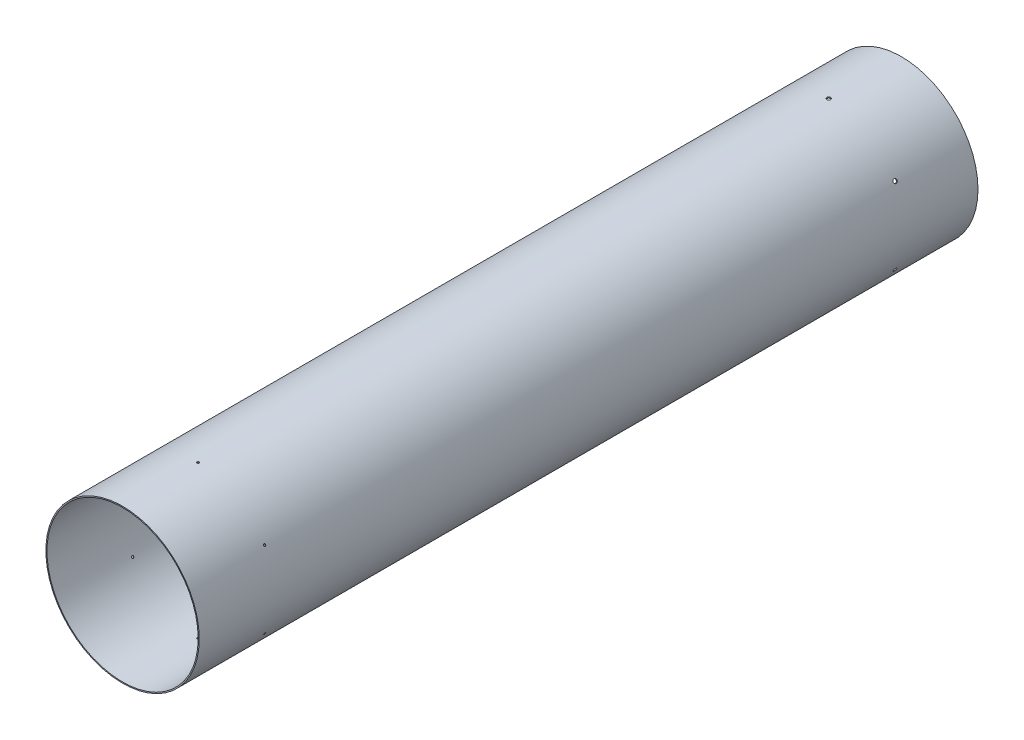
SolidWorks part; units mm, degrees
ref_plane "Front Plane" through (0, 0, 0) normal (0, 0, 1) x (1, 0, 0)
ref_plane "Top Plane" through (0, 0, 0) normal (0, 1, 0) x (1, 0, 0)
ref_plane "Right Plane" through (0, 0, 0) normal (1, 0, 0) x (0, 0, -1)
sketch "Sketch1" plane through (0, 0, 0) normal (0, 0, 1) x (1, 0, 0)
  circle A0 centre (0, 0) radius 79.375
  circle A1 centre (0, 0) radius 80.518
  dimension "D1" = 158.75
  dimension "D2" = 1.143
extrude "Boss-Extrude1" add sketch "Sketch1" along normal blind 817.5625
ref_plane "Plane1" through (0, 80.518, 0) normal (0, 1, 0) x (1, 0, 0)
sketch "Sketch2" plane through (0, 80.518, 0) normal (0, 1, 0) x (1, 0, 0)
  line L0 (80.518, 0) -> (-80.518, 0) construction
  point P0 (0, -76.2)
  dimension "D1" = 76.2
hole_wizard "Tap Drill for #10-32 Tap1" positions "Sketch3" profile "Sketch4" hole size "#10-32" standard "ANSI Inch"
sketch "Sketch3" plane through (0, 80.518, 0) normal (0, 1, 0) x (1, 0, 0)
  point P0 (0, -76.2)
sketch "Sketch4" plane through (0, 80.518, 76.2) normal (1, 0, 0) x (0, 0, 1)
  line L0 (0, 0) -> (0, 1.143)
  line L1 (0, 1.143) -> (2.0193, 1.143)
  line L2 (2.0193, 1.143) -> (2.0193, 0)
  line L5 (2.0193, 0) -> (0, 0)
  line L11 (0, -6.35) -> (0, 107.95) construction
  dimension "Thru Hole Dia." = 4.0386
  dimension "Thru Hole Depth" = 1.143
sketch "Sketch5" plane through (0, 80.518, 0) normal (0, 1, 0) x (1, 0, 0)
  line L0 (-80.518, -817.5625) -> (80.518, -817.5625) construction
  point P0 (0, -738.1875)
  dimension "D1" = 79.375
hole_wizard "Tap Drill for #4-40 Tap1" positions "Sketch6" profile "Sketch7" hole size "#4-40" standard "ANSI Inch"
sketch "Sketch6" plane through (0, 80.518, 0) normal (0, 1, 0) x (1, 0, 0)
  point P0 (0, -738.1875)
sketch "Sketch7" plane through (0, 80.518, 738.1875) normal (1, 0, 0) x (0, 0, 1)
  line L0 (0, 0) -> (0, 1.143)
  line L1 (0, 1.143) -> (1.1303, 1.143)
  line L2 (1.1303, 1.143) -> (1.1303, 0)
  line L5 (1.1303, 0) -> (0, 0)
  line L11 (0, -6.35) -> (0, 107.95) construction
  dimension "Thru Hole Dia." = 2.2606
  dimension "Thru Hole Depth" = 1.143
pattern_circular "CirPattern1" count 6 over 360 about axis through (0, 0, 817.5625) along (0, 0, 1) of "Tap Drill for #10-32 Tap1", "Tap Drill for #4-40 Tap1"
